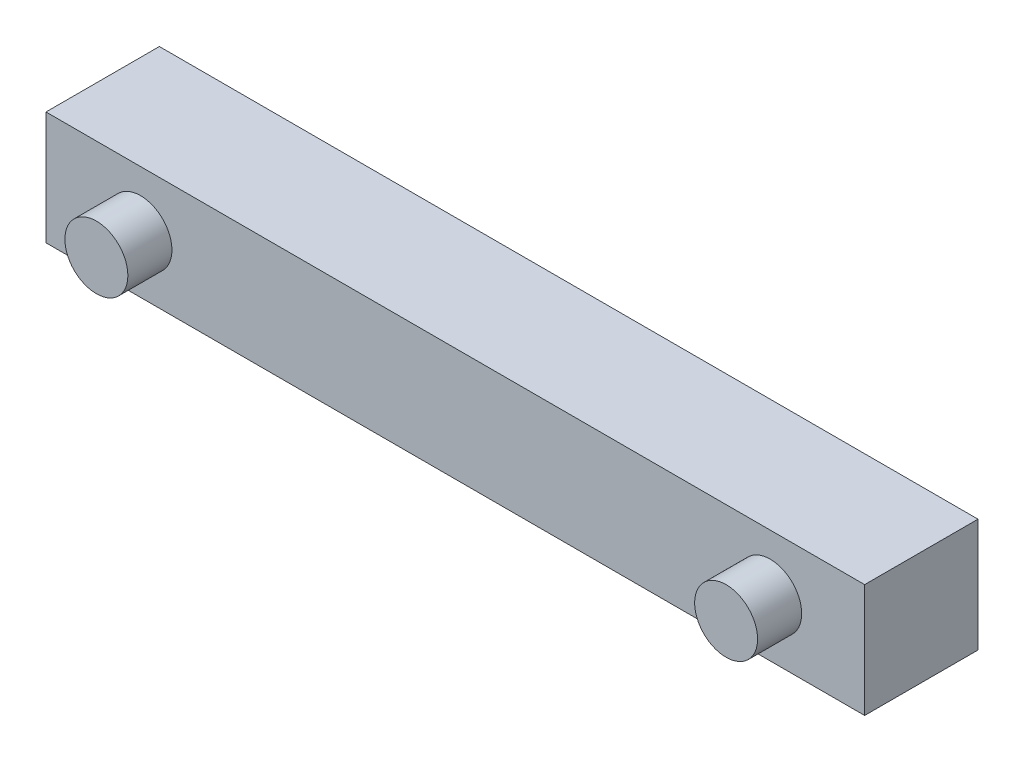
SolidWorks part; units mm, degrees
ref_plane "Front Plane" through (0, 0, 0) normal (0, 0, 1) x (1, 0, 0)
ref_plane "Top Plane" through (0, 0, 0) normal (0, 1, 0) x (1, 0, 0)
ref_plane "Right Plane" through (0, 0, 0) normal (1, 0, 0) x (0, 0, -1)
sketch "Sketch1" plane through (0, 0, 0) normal (0, 0, 1) x (1, 0, 0)
  line L0 (0, 0) -> (1651, 0)
  line L1 (1651, 0) -> (1651, 228.6)
  line L2 (1651, 228.6) -> (0, 228.6)
  line L3 (0, 228.6) -> (0, 0)
  dimension "D1" = 1651
  dimension "D2" = 228.6
extrude "Boss-Extrude1" add sketch "Sketch1" along normal blind 228.6
sketch "Sketch2" plane through (0, 0, 228.6) normal (0, 0, 1) x (1, 0, 0)
  line L0 (825.5, 228.6) -> (825.5, -100.4804) construction
  line L1 (1651, 228.6) -> (0, 228.6) construction
  circle A0 centre (190.5, 114.3) radius 63.5
  circle A1 centre (1460.5, 114.3) radius 63.5
extrude "Boss-Extrude2" add sketch "Sketch2" along normal blind 88.9
